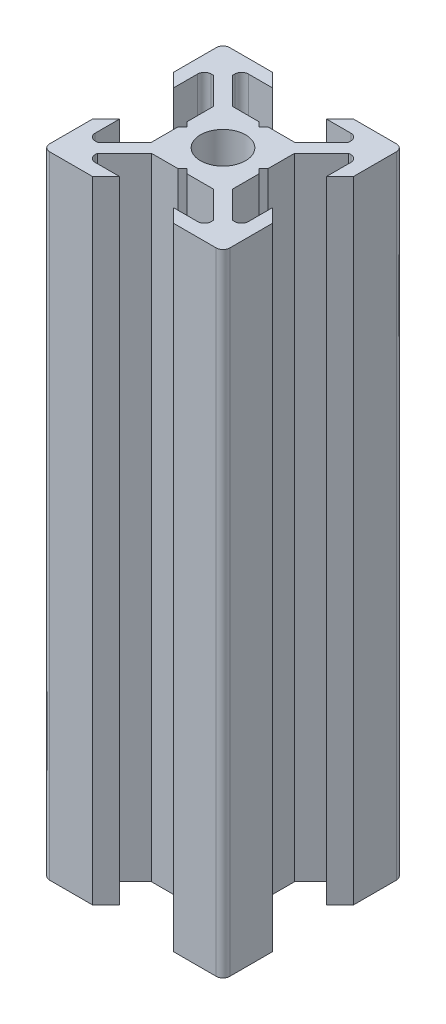
SolidWorks part; units mm, degrees
ref_plane "Face" through (0, 0, 0) normal (0, 0, 1) x (1, 0, 0)
ref_plane "Dessus" through (0, 0, 0) normal (0, 1, 0) x (1, 0, 0)
ref_plane "Droite" through (0, 0, 0) normal (1, 0, 0) x (0, 0, -1)
sketch "Esquisse1" plane through (0, 0, 0) normal (0, 1, 0) x (1, 0, 0)
  line L0 (0, 0) -> (0, 10) construction
  line L1 (0, 0) -> (-10, 0) construction
  line L2 (-10, 0) -> (-10, 10) construction
  line L3 (-10, 10) -> (0, 10) construction
  line L4 (0, 4) -> (-0.5, 4.5)
  line L5 (-0.5, 4.5) -> (-3.4393, 4.5)
  line L6 (-3.4393, 4.5) -> (-6.4393, 7.5)
  line L7 (-6.4393, 7.5) -> (-6.4393, 8.5)
  line L8 (-6.4393, 8.5) -> (-3, 8.5)
  line L9 (-3, 8.5) -> (-4.5, 10)
  line L10 (-4.5, 10) -> (-10, 10)
  line L11 (0, 0) -> (-10, 10) construction
  line L12 (-10, 4.5) -> (-10, 10)
  line L13 (-8.5, 3) -> (-10, 4.5)
  line L14 (-8.5, 6.4393) -> (-8.5, 3)
  line L15 (-7.5, 6.4393) -> (-8.5, 6.4393)
  line L16 (-4.5, 3.4393) -> (-7.5, 6.4393)
  line L17 (-4.5, 0.5) -> (-4.5, 3.4393)
  line L18 (-4, 0) -> (-4.5, 0.5)
  line L19 (0, -4) -> (-0.5, -4.5)
  line L20 (-0.5, -4.5) -> (-3.4393, -4.5)
  line L21 (-4, 0) -> (-4.5, -0.5)
  line L22 (-4.5, -0.5) -> (-4.5, -3.4393)
  line L23 (-4.5, -3.4393) -> (-7.5, -6.4393)
  line L24 (-3.4393, -4.5) -> (-6.4393, -7.5)
  line L25 (-3, -8.5) -> (-4.5, -10)
  line L26 (-6.4393, -8.5) -> (-3, -8.5)
  line L27 (-6.4393, -7.5) -> (-6.4393, -8.5)
  line L28 (-7.5, -6.4393) -> (-8.5, -6.4393)
  line L29 (-4.5, -10) -> (-10, -10)
  line L30 (-10, -4.5) -> (-10, -10)
  line L31 (-8.5, -3) -> (-10, -4.5)
  line L32 (-8.5, -6.4393) -> (-8.5, -3)
  line L33 (8.5, -6.4393) -> (8.5, -3)
  line L34 (8.5, -3) -> (10, -4.5)
  line L35 (10, -4.5) -> (10, -10)
  line L36 (4.5, -10) -> (10, -10)
  line L37 (7.5, -6.4393) -> (8.5, -6.4393)
  line L38 (6.4393, -7.5) -> (6.4393, -8.5)
  line L39 (6.4393, -8.5) -> (3, -8.5)
  line L40 (3, -8.5) -> (4.5, -10)
  line L41 (3.4393, -4.5) -> (6.4393, -7.5)
  line L42 (4.5, -3.4393) -> (7.5, -6.4393)
  line L43 (4.5, -0.5) -> (4.5, -3.4393)
  line L44 (4, 0) -> (4.5, -0.5)
  line L45 (0.5, -4.5) -> (3.4393, -4.5)
  line L46 (0, -4) -> (0.5, -4.5)
  line L47 (4, 0) -> (4.5, 0.5)
  line L48 (4.5, 0.5) -> (4.5, 3.4393)
  line L49 (4.5, 3.4393) -> (7.5, 6.4393)
  line L50 (7.5, 6.4393) -> (8.5, 6.4393)
  line L51 (8.5, 6.4393) -> (8.5, 3)
  line L52 (8.5, 3) -> (10, 4.5)
  line L53 (10, 4.5) -> (10, 10)
  line L54 (4.5, 10) -> (10, 10)
  line L55 (3, 8.5) -> (4.5, 10)
  line L56 (6.4393, 8.5) -> (3, 8.5)
  line L57 (6.4393, 7.5) -> (6.4393, 8.5)
  line L58 (3.4393, 4.5) -> (6.4393, 7.5)
  line L59 (0.5, 4.5) -> (3.4393, 4.5)
  line L60 (0, 4) -> (0.5, 4.5)
  circle A0 centre (0, 0) radius 2.5
  dimension "D10" = 5
  dimension "D1" = 10
  dimension "D2" = 45
  dimension "D3" = 45
  dimension "D4" = 1.5
  dimension "D5" = 7
  dimension "D6" = 1
  dimension "D7" = 4.5
  dimension "D8" = 0.5
  dimension "D9" = 0.75
extrude "Extrusion1" add sketch "Esquisse1" along normal blind 70
fillet "Congé1" radius 0.75 12 edges at (-8.5, 35, -6.4393) (-6.4393, 35, -8.5) (8.5, 35, -6.4393) (6.4393, 35, -8.5) (-8.5, 35, 6.4393) (-6.4393, 35, 8.5) (8.5, 35, 6.4393) (6.4393, 35, 8.5) (10, 35, -10) (-10, 35, -10) (-10, 35, 10) (10, 35, 10)
